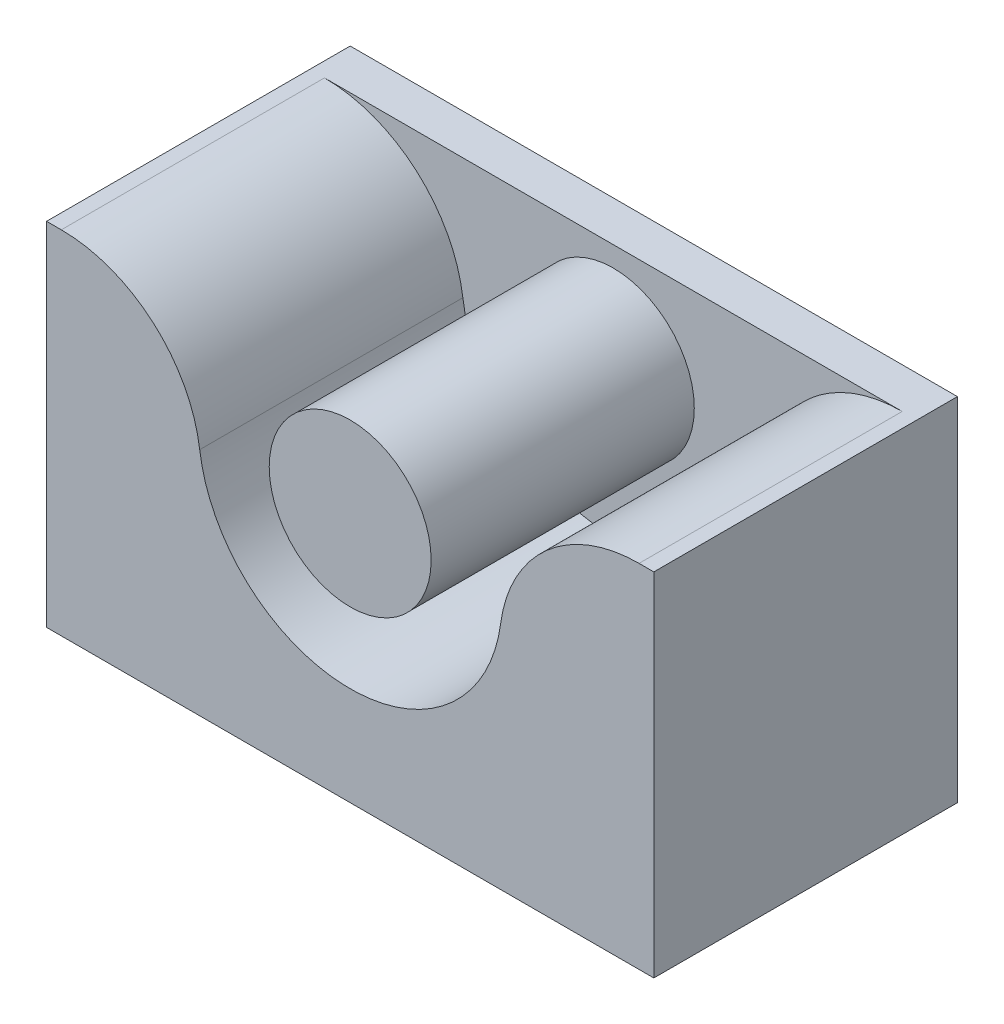
SolidWorks part; units mm, degrees
ref_plane "Alzado" through (0, 0, 0) normal (0, 0, 1) x (1, 0, 0)
ref_plane "Planta" through (0, 0, 0) normal (0, 1, 0) x (1, 0, 0)
ref_plane "Vista lateral" through (0, 0, 0) normal (1, 0, 0) x (0, 0, -1)
sketch "Croquis2" plane through (0, 0, 0) normal (0, 0, 1) x (1, 0, 0)
  line L0 (-15, 5) -> (15, 5)
  line L1 (-15, 5) -> (-15, -12.375)
  line L2 (-15, -12.375) -> (15, -12.375)
  line L3 (15, -12.375) -> (15, 5)
  dimension "D4" = 30
  dimension "D5" = 30
  dimension "D6" = 90
  dimension "D7" = 90
extrude "Saliente-Extruir1" add sketch "Croquis2" along normal blind 2
sketch "Croquis3" plane through (0, 0, 2) normal (0, 0, 1) x (1, 0, 0)
  line L0 (15, 5) -> (-15, 5) construction
  line L1 (-15, 5) -> (-14.2713, 5)
  line L2 (-15, 5) -> (-15, -12.375)
  line L3 (-15, -12.375) -> (15, -12.375)
  line L4 (15, 5) -> (15, -12.375)
  line L5 (14.2713, 5) -> (15, 5)
  line L6 (0, 6.4136) -> (0, 0) construction
  circle A0 centre (0, 0) radius 4
  arc A1 (-7.4346, -0.9881) -> (7.4346, -0.9881) centre (0, 0) ccw
  arc A2 (7.4346, -0.9881) -> (14.2713, 5) centre (14.2713, -1.8968) cw
  arc A3 (-7.4346, -0.9881) -> (-14.2713, 5) centre (-14.2713, -1.8968) ccw
  dimension "D1" = 15
  dimension "D2" = 8
  dimension "D3" = 30
extrude "Saliente-Extruir2" add sketch "Croquis3" along normal blind 13
